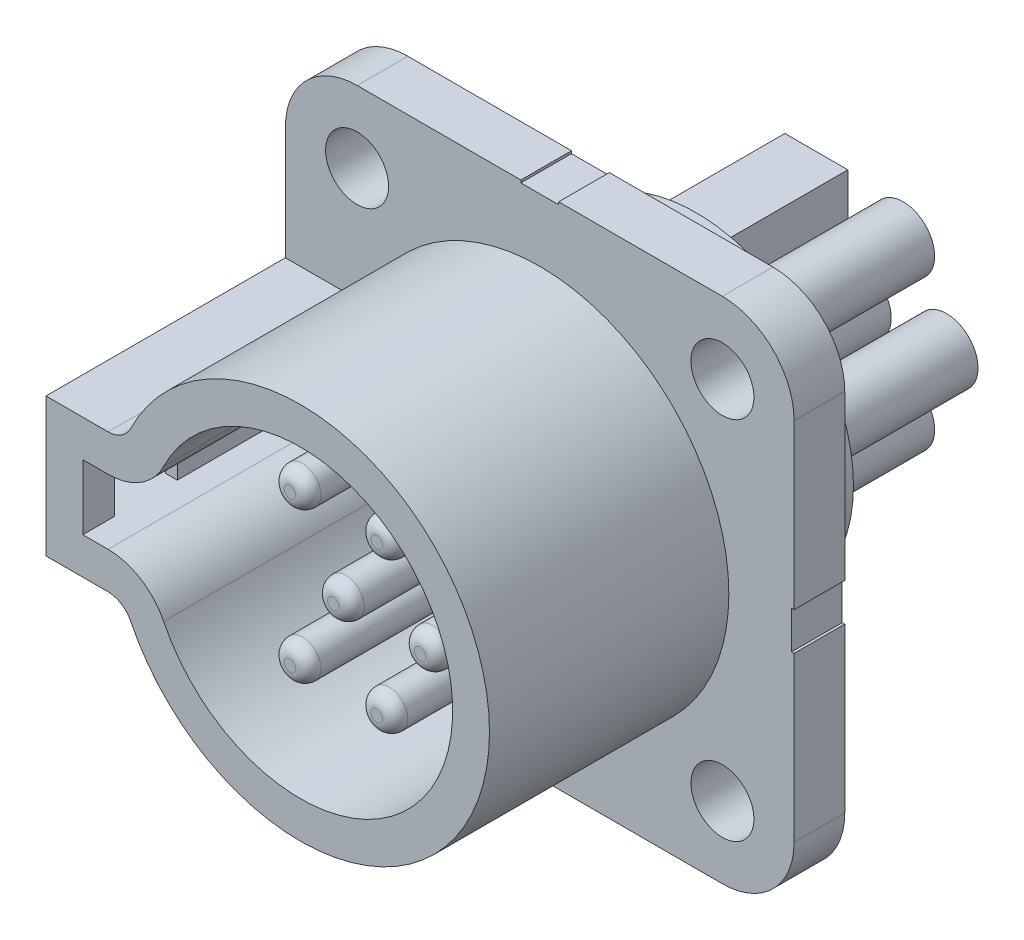
SolidWorks part; units mm, degrees
ref_plane "Front Plane" through (0, 0, 0) normal (0, 0, 1) x (1, 0, 0)
ref_plane "Top Plane" through (0, 0, 0) normal (0, 1, 0) x (1, 0, 0)
ref_plane "Right Plane" through (0, 0, 0) normal (1, 0, 0) x (0, 0, -1)
sketch "Sketch1" plane through (0, 0, 0) normal (0, 0, 1) x (1, 0, 0)
  line L1 (-10.095, 10.095) -> (10.095, 10.095)
  line L2 (-10.095, 10.095) -> (-10.095, -10.095)
  line L3 (-10.095, -10.095) -> (10.095, -10.095)
  line L4 (10.095, 10.095) -> (10.095, -10.095)
  line L5 (-10.095, 10.095) -> (10.095, -10.095) construction
  line L6 (-10.095, -10.095) -> (10.095, 10.095) construction
  point P0 (0, 0)
  dimension "D1" = 20.19
  dimension "D2" = 20.19
extrude "Boss-Extrude1" add sketch "Sketch1" along normal blind 2.01
sketch "Sketch2" plane through (0, 0, 2.01) normal (0, 0, 1) x (1, 0, 0)
  line L0 (0, 0) -> (0, 10.095) construction
  line L1 (10.095, 10.095) -> (-10.095, 10.095) construction
  line L2 (0, 0) -> (-10.095, 0) construction
  line L3 (-10.095, 10.095) -> (-10.095, -10.095) construction
  circle A0 centre (-7.25, 7.25) radius 1.25
  circle A1 centre (7.25, 7.25) radius 1.25
  circle A2 centre (7.25, -7.25) radius 1.25
  circle A3 centre (-7.25, -7.25) radius 1.25
  dimension "D1" = 2.5
  dimension "D2" = 7.25
  dimension "D3" = 7.25
extrude "Cut-Extrude1" cut sketch "Sketch2" against normal up to surface (2.01 mm away) up to face at (0, 0, 0)
fillet "Fillet1" radius 2.85 4 edges at (10.095, -10.095, 1.005) (-10.095, -10.095, 1.005) (10.095, 10.095, 1.005) (-10.095, 10.095, 1.005)
sketch "Sketch4" plane through (0, 0, 2.01) normal (0, 0, 1) x (1, 0, 0)
  line L0 (-10.095, -2.7495) -> (-10.095, 2.7495)
  line L1 (-10.095, 7.245) -> (-10.095, -7.245) construction
  line L2 (-10.095, 2.7495) -> (-7.6339, 2.7495)
  line L3 (-10.095, 0) -> (11.2357, 0) construction
  line L4 (-10.095, -2.7495) -> (-7.6339, -2.7495)
  line L5 (-8.635, -1.2895) -> (-8.635, 1.2895)
  line L6 (-8.635, 1.2895) -> (-7.6339, 1.2895)
  line L7 (-8.635, -1.2895) -> (-7.6339, -1.2895)
  line L8 (0, 10.095) -> (0, -11.6505) construction
  line L9 (7.245, 10.095) -> (-7.245, 10.095) construction
  line L10 (0, 6.045) -> (3.3385, 6.045) construction
  line L11 (0, -6.045) -> (3.3385, -6.045) construction
  line L12 (0, -7.505) -> (3.9298, -7.505) construction
  line L13 (0, 7.505) -> (4.2254, 7.505) construction
  arc A0 (-6.7363, 3.3086) -> (-6.7363, -3.3086) centre (0, 0) cw
  arc A1 (-6.7363, 3.3086) -> (-7.6339, 2.7495) centre (-7.6339, 3.7495) cw
  arc A2 (-6.7363, -3.3086) -> (-7.6339, -2.7495) centre (-7.6339, -3.7495) ccw
  arc A3 (-5.4259, 2.665) -> (-7.6339, 1.2895) centre (-7.6339, 3.7495) cw
  arc A4 (-5.4259, 2.665) -> (-5.4259, -2.665) centre (0, 0) cw
  arc A5 (-5.4259, -2.665) -> (-7.6339, -1.2895) centre (-7.6339, -3.7495) ccw
  dimension "D1" = 1
  dimension "D3" = 15.01
  dimension "D4" = 12.09
extrude "Boss-Extrude2" add sketch "Sketch4" along normal blind 9.5
sketch "Sketch5" plane through (-10.095, 0, 0) normal (-1, 0, 0) x (0, 0, 1)
  line L0 (0, 7.245) -> (0, -7.245) construction
  line L1 (0, 1.2895) -> (10.26, 1.2895)
  line L2 (0, 1.2895) -> (0, -1.2895)
  line L3 (0, -1.2895) -> (10.26, -1.2895)
  line L4 (10.26, 1.2895) -> (10.26, -1.2895)
  line L6 (0, 0) -> (-1.0293, 0) construction
  line L7 (11.51, 2.7495) -> (11.51, -2.7495) construction
  line L8 (11.51, 2.7495) -> (2.01, 2.7495) construction
  line L9 (11.51, -2.7495) -> (2.01, -2.7495) construction
  dimension "D1" = 1.25
  dimension "D2" = 1.46
  dimension "D3" = 1.46
extrude "Cut-Extrude2" cut sketch "Sketch5" against normal blind 1
sketch "Sketch6" plane through (-9.095, 0, 0) normal (-1, 0, 0) x (0, 0, 1)
  line L0 (0, -1.2895) -> (10.26, -1.2895) construction
  line L1 (10.26, 1.2895) -> (7.76, 1.2895)
  line L2 (10.26, 1.2895) -> (10.26, -1.2895)
  line L3 (10.26, -1.2895) -> (7.76, -1.2895)
  line L4 (7.76, 1.2895) -> (7.76, -1.2895)
  dimension "D1" = 2.5
extrude "Cut-Extrude3" cut sketch "Sketch6" against normal up to next
sketch "Sketch7" plane through (0, 0, 0) normal (0, 0, -1) x (-1, 0, 0)
  circle A0 centre (0, 0) radius 6.25
  dimension "D1" = 12.5
extrude "Boss-Extrude3" add sketch "Sketch7" along normal blind 4.19
sketch "Sketch8" plane through (0, 0, 2.01) normal (0, 0, 1) x (1, 0, 0)
  line L0 (-3.445, 0) -> (5.0962, 0) construction
  circle A0 centre (0, 0) radius 0.73
  circle A2 centre (3.445, 0) radius 0.73
  circle A3 centre (1.7225, 2.9835) radius 0.73
  circle A4 centre (-1.7225, 2.9835) radius 0.73
  circle A5 centre (1.7225, -2.9835) radius 0.73
  circle A6 centre (-1.7225, -2.9835) radius 0.73
  dimension "D1" = 1.46
extrude "Boss-Extrude4" add sketch "Sketch8" along normal blind 8.19 and the other way blind 7
fillet "Fillet2" radius 0.5 6 edges at (-2.4525, -2.9835, 10.2) (2.4525, 2.9835, 10.2) (0.9925, -2.9835, 10.2) (4.175, 0, 10.2) (0.73, 0, 10.2) (-0.9925, 2.9835, 10.2)
sketch "Sketch9" plane through (0, 0, -4.19) normal (0, 0, -1) x (-1, 0, 0)
  line L0 (2.7225, 2.9835) -> (2.7225, 4.3134) construction
  line L1 (1.7225, 3.9835) -> (2.7225, 3.9835) construction
  line L2 (0, 0) -> (6.9156, 0) construction
  line L3 (0.7225, 1.9835) -> (2.7225, 1.9835)
  line L4 (0.7225, 1.9835) -> (0.7225, 3.9835)
  line L5 (0.7225, 3.9835) -> (2.7225, 3.9835)
  line L6 (2.7225, 1.9835) -> (2.7225, 3.9835)
  line L7 (0.7225, 1.9835) -> (2.7225, 3.9835) construction
  line L8 (0.7225, 3.9835) -> (2.7225, 1.9835) construction
  line L9 (0.7225, -3.9835) -> (2.7225, -3.9835)
  line L10 (0.7225, -1.9835) -> (0.7225, -3.9835)
  line L11 (2.7225, -1.9835) -> (2.7225, -3.9835)
  line L12 (0.7225, -1.9835) -> (2.7225, -1.9835)
  circle A0 centre (-1.7225, 2.9835) radius 1
  circle A2 centre (0, 0) radius 1
  circle A3 centre (-3.445, 0) radius 1
  circle A4 centre (-1.7225, -2.9835) radius 1
  circle A5 centre (-1.7225, -2.9835) radius 1
  point P0 (-1.7225, 2.9835)
  point P1 (1.7225, 2.9835)
  point P3 (-3.445, 0)
  point P5 (0, 0)
  point P7 (-1.7225, -2.9835)
  point P9 (1.7225, -2.9835)
  dimension "D1" = 2
  dimension "D2" = 2
  dimension "D3" = 2
  dimension "D5" = 2
  dimension "D4" = 2.9835
  dimension "D6" = 2
extrude "Extrude-Thin1" add sketch "Sketch9" along normal blind 6.5 thin
sketch "Sketch10" plane through (0, 10.095, 0) normal (0, 1, 0) x (1, 0, 0)
  line L0 (7.245, 0) -> (-7.245, 0) construction
  line L1 (-0.75, 0) -> (0.75, 0)
  line L2 (-0.75, 0) -> (-0.75, -2.01)
  line L3 (-0.75, -2.01) -> (0.75, -2.01)
  line L4 (0.75, 0) -> (0.75, -2.01)
  line L5 (7.245, -2.01) -> (-7.245, -2.01) construction
  line L6 (0, 4.99) -> (0, -4.274) construction
  line L7 (0.73, 4.99) -> (-0.73, 4.99) construction
  point P10 (0, -2.01)
  dimension "D1" = 1.5
  dimension "D2" = 0
extrude "Cut-Extrude4" cut sketch "Sketch10" against normal blind 0.1
sketch "Sketch12" plane through (10.095, 0, 0) normal (1, 0, 0) x (0, 0, -1)
  line L0 (-11.51, 0) -> (5.9037, 0)
  line L1 (-11.51, 7.505) -> (-11.51, -7.505) construction
  line L2 (0, -7.245) -> (0, 7.245) construction
  line L3 (-2.01, 0.75) -> (0, 0.75)
  line L4 (-2.01, 0.75) -> (-2.01, -0.75)
  line L5 (-2.01, -0.75) -> (0, -0.75)
  line L6 (0, 0.75) -> (0, -0.75)
  line L7 (-2.01, 0.75) -> (0, -0.75) construction
  line L8 (-2.01, -0.75) -> (0, 0.75) construction
  line L9 (-2.01, -7.245) -> (-2.01, 7.245) construction
  point P5 (-1.005, 0)
  dimension "D1" = 1.5
extrude "Cut-Extrude5" cut sketch "Sketch12" against normal blind 0.1 contours L4 L5 L6 L3
equation "\"D2@Sketch1\"=\"D1@Sketch1\""
equation "\"D3@Sketch5\"=\"D2@Sketch5\""
equation "\"D2@Sketch9\"=\"D1@Sketch9\""
equation "\"D3@Sketch9\"=\"D1@Sketch9\""
equation "\"D5@Sketch9\"=\"D1@Sketch9\""
